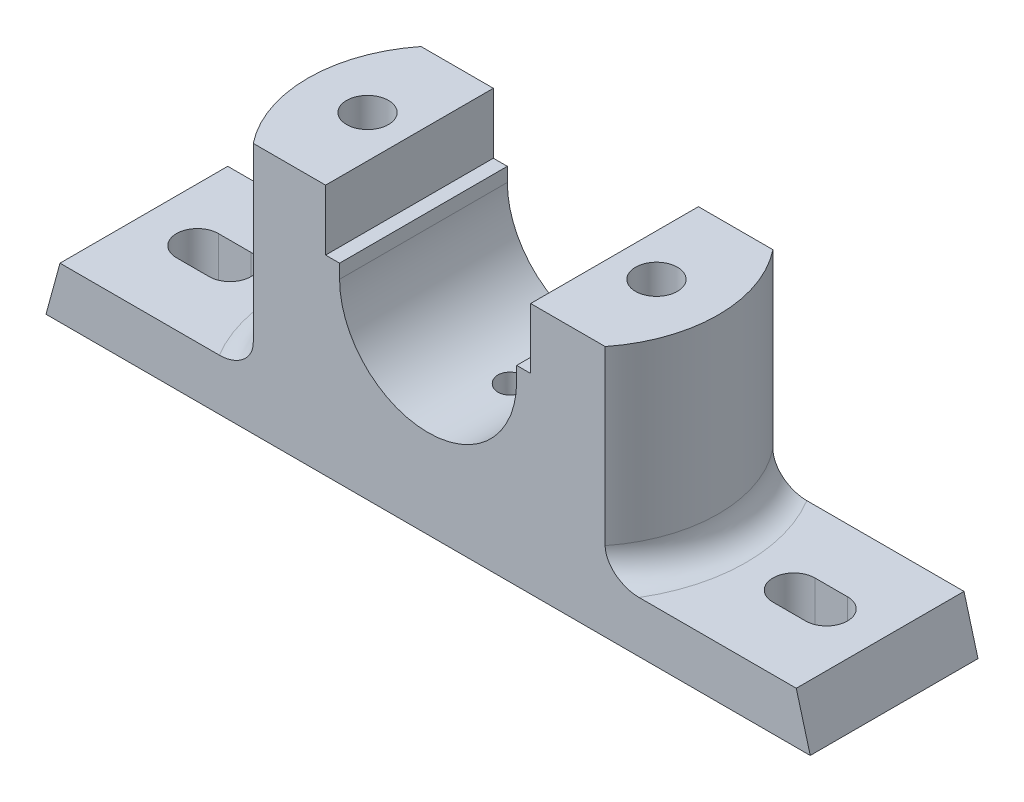
SolidWorks part; units mm, degrees
ref_plane "Front Plane" through (0, 0, 0) normal (0, 0, 1) x (1, 0, 0)
ref_plane "Top Plane" through (0, 0, 0) normal (0, 1, 0) x (1, 0, 0)
ref_plane "Right Plane" through (0, 0, 0) normal (1, 0, 0) x (0, 0, -1)
sketch "Sketch1" plane through (0, 0, 0) normal (0, 0, 1) x (1, 0, 0)
  line L0 (0, 55.2726) -> (0, -38.8402) construction
  line L1 (-65.2268, 0) -> (80.9789, 0) construction
  line L2 (50, -27) -> (79, -27)
  line L3 (-19, 0) -> (-19, 3)
  line L4 (-22, 16) -> (-50, 16)
  line L5 (-50, 16) -> (-50, -27)
  line L6 (-50, -27) -> (-79, -27)
  line L7 (-79, -27) -> (-82, -38)
  line L8 (-82, -38) -> (82, -38)
  line L9 (19, 3) -> (19, 0)
  line L10 (-19, 3) -> (-22, 3)
  line L11 (-22, 3) -> (-22, 16)
  line L12 (79, -27) -> (82, -38)
  line L14 (19, 3) -> (22, 3)
  line L15 (22, 3) -> (22, 16)
  line L16 (22, 16) -> (50, 16)
  line L17 (50, 16) -> (50, -27)
  arc A0 (-19, 0) -> (19, 0) centre (0, 0) ccw
  dimension "D1" = 50
  dimension "D8" = 16
  dimension "D7" = 19
  dimension "D2" = 13
  dimension "D3" = 43
  dimension "D4" = 3
  dimension "D5" = 164
  dimension "D6" = 11
  dimension "D9" = 44
extrude "Boss-Extrude2" add sketch "Sketch1" along normal blind 36 contours L4 L5 L6 L7 L8 L12 L2 L17 L16 L15 L14 L9 A0 L3 L10 L11
sketch "Sketch11" plane through (0, 16, 0) normal (0, 1, 0) x (1, 0, 0)
  line L3 (-50, 0) -> (-50, -36)
  line L4 (-50, -36) -> (-37.5233, -36)
  line L5 (-22, -36) -> (-50, -36) construction
  line L6 (-50, 0) -> (-37.5233, 0)
  line L8 (-22, 0) -> (-50, 0) construction
  arc A0 (-37.5233, -36) -> (-37.5233, 0) centre (-14.7857, -18) cw
  dimension "D1" = 29
extrude "Cut-Extrude1" cut sketch "Sketch11" against normal blind 43
fillet "Fillet1" radius 6 1 edges at (-43.7857, -27, 18)
sketch "Sketch12" plane through (0, 16, 0) normal (0, 1, 0) x (1, 0, 0)
  line L0 (37.995, 0) -> (50, 0)
  line L1 (22, 0) -> (50, 0) construction
  line L2 (50, 0) -> (50, -36)
  line L3 (50, -36) -> (37.995, -36)
  line L4 (22, -36) -> (50, -36) construction
  arc A0 (37.995, 0) -> (37.995, -36) centre (15.2573, -18) cw
  dimension "D1" = 29
extrude "Cut-Extrude2" cut sketch "Sketch12" against normal blind 43
fillet "Fillet2" radius 6 1 edges at (44.2573, -27, 18)
hole_wizard "Ø6.0mm Dowel Hole1" positions "3DSketch1" profile "Sketch14" hole size "Ø6.0" standard "ANSI Metric"
sketch3d "3DSketch1"
  point P0 (0, -19, 18)
  dimension "D1" = 0
  dimension "D2" = 18
sketch "Sketch14" plane through (0, -19, 18) normal (1, 0, 0) x (0, 0, 1)
  line L0 (0, 0) -> (0, 7.8026)
  line L1 (0, 7.8026) -> (3, 6)
  line L2 (3, 6) -> (3, 0)
  line L5 (3, 0) -> (0, 0)
  line L10 (0, 7.8026) -> (-3, 6) construction
  line L11 (0, -6.35) -> (0, 107.95) construction
  dimension "Hole Dia." = 6
  dimension "Hole Depth" = 6
  dimension "Drill Angle" = 118
hole_wizard "Ø6.0mm Dowel Hole3" positions "Sketch20" profile "Sketch19" hole size "Ø6.0" standard "ANSI Metric"
sketch "Sketch20" plane through (0, 16, 0) normal (0, 1, 0) x (1, 0, 0)
  line L0 (-29.7, 0) -> (29.7, 0) construction
  line L1 (0, -19.8) -> (0, 19.8) construction
  point P0 (-31, -18)
  dimension "D1" = 18
  dimension "D2" = 31
sketch "Sketch19" plane through (-31, 16, 18) normal (1, 0, 0) x (0, 0, 1)
  line L0 (0, 0) -> (0, 48.7039)
  line L1 (0, 48.7039) -> (4.5, 46)
  line L2 (4.5, 46) -> (4.5, 0)
  line L5 (4.5, 0) -> (0, 0)
  line L10 (0, 48.7039) -> (-4.5, 46) construction
  line L11 (0, -6.35) -> (0, 107.95) construction
  dimension "Hole Dia." = 9
  dimension "Hole Depth" = 46
  dimension "Drill Angle" = 118
sketch "Sketch23" plane through (0, -38, 0) normal (0, -1, 0) x (1, 0, 0)
  line L0 (-82, 36) -> (-82, 0) construction
  line L1 (-21, 28) -> (-41, 28)
  line L2 (-21, 28) -> (-21, 8)
  line L3 (-21, 8) -> (-41, 8)
  line L4 (-41, 28) -> (-41, 8)
  line L5 (-21, 28) -> (-41, 8) construction
  line L6 (-21, 8) -> (-41, 28) construction
  line L8 (-82, 36) -> (82, 36) construction
  point P0 (-31, 18)
  dimension "D1" = 20
  dimension "D2" = 20
  dimension "D3" = 51
  dimension "D4" = 18
extrude "Cut-Extrude4" cut sketch "Sketch23" against normal blind 8
mirror "Mirror1" about plane through (0, 0, 0) normal (1, 0, 0) of "Ø6.0mm Dowel Hole3", "Cut-Extrude4"
sketch "Sketch25" plane through (0, -27, 0) normal (0, 1, 0) x (1, 0, 0)
  line L0 (-67.5, -18) -> (-60.5, -18) construction
  line L1 (-67.5, -13.5) -> (-60.5, -13.5)
  line L2 (-67.5, -22.5) -> (-60.5, -22.5)
  line L3 (-44.8024, -36) -> (-79, -36) construction
  line L4 (-79, -36) -> (-79, 0) construction
  arc A0 (-67.5, -13.5) -> (-67.5, -22.5) centre (-67.5, -18) ccw
  arc A1 (-60.5, -22.5) -> (-60.5, -13.5) centre (-60.5, -18) ccw
  point P2 (-64, -18)
  dimension "D1" = 16
  dimension "D2" = 18
  dimension "D3" = 15
  dimension "D4" = 9
extrude "Cut-Extrude5" cut sketch "Sketch25" against normal through all
mirror "Mirror2" about plane through (0, 0, 0) normal (1, 0, 0) of "Cut-Extrude5"
